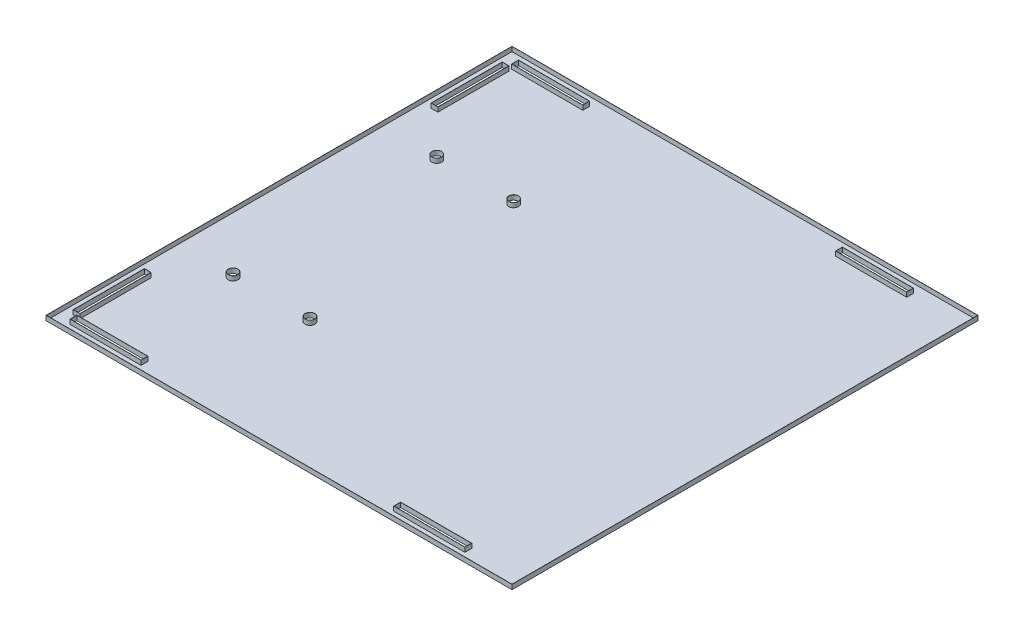
SolidWorks part; units mm, degrees
ref_plane "Front Plane" through (0, 0, 0) normal (0, 0, 1) x (1, 0, 0)
ref_plane "Top Plane" through (0, 0, 0) normal (0, 1, 0) x (1, 0, 0)
ref_plane "Right Plane" through (0, 0, 0) normal (1, 0, 0) x (0, 0, -1)
sketch "Sketch1" plane through (0, 0, 0) normal (0, 1, 0) x (1, 0, 0)
  line L1 (0, 63.5) -> (254, 63.5)
  line L2 (0, 63.5) -> (0, -63.5)
  line L3 (0, -63.5) -> (254, -63.5)
  line L4 (254, 63.5) -> (254, -63.5)
  line L5 (8.382, 58.674) -> (46.99, 58.674)
  line L6 (8.382, 58.674) -> (8.382, 55.118)
  line L7 (8.382, 55.118) -> (46.99, 55.118)
  line L8 (46.99, 58.674) -> (46.99, 55.118)
  line L9 (184.912, 58.674) -> (223.52, 58.674)
  line L10 (184.912, 58.674) -> (184.912, 55.118)
  line L11 (184.912, 55.118) -> (223.52, 55.118)
  line L12 (223.52, 58.674) -> (223.52, 55.118)
  line L13 (4.826, 53.34) -> (8.382, 53.34)
  line L14 (4.826, 53.34) -> (4.826, 14.732)
  line L15 (4.826, 14.732) -> (8.382, 14.732)
  line L16 (8.382, 53.34) -> (8.382, 14.732)
  dimension "D1" = 127
  dimension "D2" = 254
  dimension "D3" = 3.556
  dimension "D4" = 38.608
  dimension "D5" = 38.608
  dimension "D6" = 3.556
  dimension "D7" = 137.922
  dimension "D8" = 8.382
  dimension "D9" = 8.382
  dimension "D10" = 46.99
  dimension "D11" = 3.556
  dimension "D12" = 38.608
  dimension "D13" = 8.382
  dimension "D14" = 48.768
extrude "Boss-Extrude1" add sketch "Sketch1" along normal blind 2.54
hole_wizard "#7 (0.201) Diameter Hole1" positions "3DSketch1" profile "Sketch3" hole size "#7" standard "ANSI Inch" end condition through all
sketch3d "3DSketch1"
  line L0 (254, 2.54, -63.5) -> (0, 2.54, -63.5) construction
  line L1 (0, 2.54, -63.5) -> (0, 2.54, 63.5) construction
  point P0 (30.48, 2.54, 7.9756)
  point P2 (72.39, 2.54, 7.9756)
  dimension "D1" = 71.4756
  dimension "D2" = 30.48
  dimension "D3" = 41.91
sketch "Sketch3" plane through (30.48, 2.54, 7.9756) normal (1, 0, 0) x (0, 0, 1)
  line L0 (0, 0) -> (0, 2.54)
  line L1 (0, 2.54) -> (2.5527, 2.54)
  line L2 (2.5527, 2.54) -> (2.5527, 0)
  line L5 (2.5527, 0) -> (0, 0)
  line L11 (0, -6.35) -> (0, 107.95) construction
  dimension "Thru Hole Dia." = 5.1054
  dimension "Thru Hole Depth" = 2.54
mirror "Mirror1" about plane through (0, 2.54, 63.5) normal (0, 0, -1) of "Boss-Extrude1", "#7 (0.201) Diameter Hole1"
shell "Shell1" thickness 0.1016
